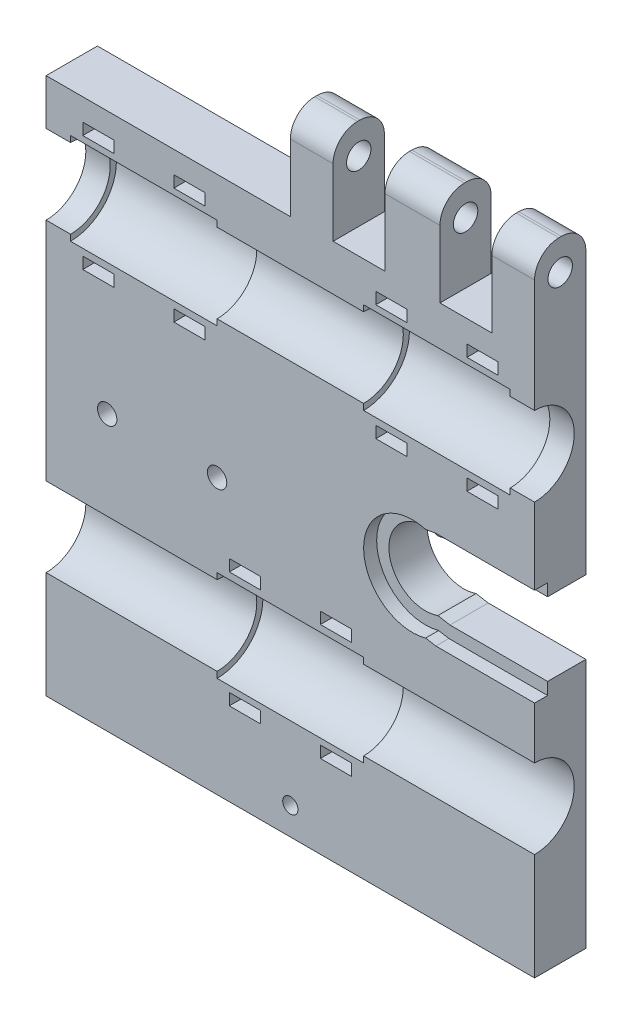
SolidWorks part; units mm, degrees
ref_plane "Front Plane" through (0, 0, 0) normal (0, 0, 1) x (1, 0, 0)
ref_plane "Top Plane" through (0, 0, 0) normal (0, 1, 0) x (1, 0, 0)
ref_plane "Right Plane" through (0, 0, 0) normal (1, 0, 0) x (0, 0, -1)
sketch "Sketch1" plane through (0, 0, 0) normal (0, 0, 1) x (1, 0, 0)
  line L1 (0, 0) -> (80, 0)
  line L2 (0, 0) -> (0, 78)
  line L3 (0, 78) -> (80, 78)
  line L4 (80, 0) -> (80, 78)
  dimension "D1" = 78
  dimension "D2" = 80
extrude "Boss-Extrude1" add sketch "Sketch1" along normal blind 8.4
sketch "Sketch2" plane through (0, 0, 8.4) normal (0, 0, 1) x (1, 0, 0)
  line L0 (0, 64) -> (80, 64)
  line L1 (0, 78) -> (0, 0) construction
  line L2 (80, 0) -> (80, 78) construction
  line L6 (80, 78) -> (0, 78) construction
  line L8 (0, 64) -> (9.5411, 64)
  line L9 (0, 64) -> (0, 70.5)
  line L10 (0, 70.5) -> (4, 70.5)
  line L12 (9.5411, 64) -> (23.4954, 64)
  line L13 (4, 70.5) -> (4, 71.5)
  line L14 (4, 71.5) -> (28, 71.5)
  line L15 (28, 70.5) -> (28, 71.5)
  line L16 (23.4954, 64) -> (54.4624, 64)
  line L18 (28, 70.5) -> (52, 70.5)
  line L20 (54.4624, 64) -> (68.2256, 64)
  line L21 (52, 70.5) -> (52, 71.5)
  line L22 (52, 71.5) -> (76, 71.5)
  line L23 (76, 70.5) -> (76, 71.5)
  line L24 (68.2256, 64) -> (80, 64)
  line L26 (76, 70.5) -> (80, 70.5)
  line L27 (80, 64) -> (80, 70.5)
  dimension "D1" = 7.5
  dimension "D2" = 14
  dimension "D3" = 6.5
  dimension "D4" = 24
  dimension "D5" = 24
  dimension "D6" = 4
  dimension "D7" = 4
revolve "Cut-Revolve1" cut sketch "Sketch2" angle 360 about L0
sketch "Sketch3" plane through (0, 0, 8.4) normal (0, 0, 1) x (1, 0, 0)
  line L0 (0, 14) -> (80, 14)
  line L1 (0, 57.5) -> (0, 0) construction
  line L2 (80, 0) -> (80, 57.5) construction
  line L3 (0, 0) -> (80, 0) construction
  line L4 (25.7093, 14) -> (47.9574, 14)
  line L5 (28, 20.5) -> (28, 21.5)
  line L6 (28, 21.5) -> (52, 21.5)
  line L7 (52, 20.5) -> (52, 21.5)
  line L8 (25.7093, 14) -> (0, 14)
  line L10 (28, 20.5) -> (0, 20.5)
  line L11 (0, 14) -> (0, 20.5)
  line L12 (47.9574, 14) -> (80, 14)
  line L14 (52, 20.5) -> (80, 20.5)
  line L15 (80, 14) -> (80, 20.5)
  dimension "D1" = 6.5
  dimension "D2" = 7.5
  dimension "D3" = 24
  dimension "D4" = 28
  dimension "D5" = 14
revolve "Cut-Revolve2" cut sketch "Sketch3" angle 360 about L0
sketch "Sketch4" plane through (0, 0, 8.4) normal (0, 0, 1) x (1, 0, 0)
  line L0 (0, 78) -> (0, 70.5) construction
  line L1 (6, 74.405) -> (11.08, 74.405)
  line L2 (6, 74.405) -> (6, 72.5)
  line L3 (6, 72.5) -> (11.08, 72.5)
  line L4 (11.08, 74.405) -> (11.08, 72.5)
  line L5 (20.92, 72.5) -> (26, 72.5)
  line L6 (20.92, 72.5) -> (20.92, 74.405)
  line L7 (20.92, 74.405) -> (26, 74.405)
  line L8 (26, 72.5) -> (26, 74.405)
  line L10 (28, 70.5) -> (28, 57.5) construction
  line L11 (80, 78) -> (0, 78) construction
  dimension "D1" = 5.08
  dimension "D2" = 5.08
  dimension "D3" = 1.905
  dimension "D4" = 1.905
  dimension "D5" = 6
  dimension "D6" = 2
  dimension "D7" = 5.5
extrude "Cut-Extrude1" cut sketch "Sketch4" against normal through all
pattern_linear "LPattern1" count 2 spacing 19 along (0, -1, 0) count 2 spacing 48 along (1, 0, 0) of "Cut-Extrude1"
sketch "Sketch5" plane through (0, 0, 8.4) normal (0, 0, 1) x (1, 0, 0)
  line L0 (28, 7.5) -> (28, 20.5) construction
  line L1 (30, 22.6) -> (35.08, 22.6)
  line L2 (30, 22.6) -> (30, 24.505)
  line L3 (30, 24.505) -> (35.08, 24.505)
  line L4 (35.08, 22.6) -> (35.08, 24.505)
  line L5 (44.92, 22.6) -> (50, 22.6)
  line L6 (44.92, 22.6) -> (44.92, 24.505)
  line L7 (44.92, 24.505) -> (50, 24.505)
  line L8 (50, 22.6) -> (50, 24.505)
  line L9 (52, 21.5) -> (52, 6.5) construction
  line L10 (28, 21.5) -> (52, 21.5) construction
  dimension "D1" = 2
  dimension "D2" = 2
  dimension "D3" = 5.08
  dimension "D4" = 5.08
  dimension "D5" = 1.1
  dimension "D6" = 1.1
  dimension "D7" = 1.905
  dimension "D8" = 1.905
extrude "Cut-Extrude2" cut sketch "Sketch5" against normal blind 8.4
pattern_linear "LPattern2" count 2 spacing 19 along (0, -1, 0) of "Cut-Extrude2"
sketch "Sketch6" plane through (0, 0, 8.4) normal (0, 0, 1) x (1, 0, 0)
  line L0 (0, 0) -> (80, 0) construction
  line L1 (80, 20.5) -> (80, 57.5) construction
  line L2 (60, 43) -> (80, 43)
  line L3 (80, 43) -> (80, 31)
  line L4 (80, 31) -> (60, 31)
  line L5 (64, 43) -> (62.0179, 42.6505)
  line L6 (64, 31) -> (62.0179, 31.3495)
  arc A0 (62.0179, 42.6505) -> (62.0179, 31.3495) centre (60, 37) ccw
  line M27 (80, 20.5) -> (80, 57.5)
  dimension "D1" = 12
  dimension "D2" = 37
  dimension "D3" = 20
  dimension "D4" = 4
  dimension "D5" = 170
  dimension "D6" = 4
  dimension "D7" = 170
extrude "Cut-Extrude3" cut sketch "Sketch6" against normal through all contours L5 A0 L6 L4 L2 M27
sketch "Sketch8" plane through (0, 0, 8.4) normal (0, 0, 1) x (1, 0, 0)
  line L12 (80, 45) -> (80, 29)
  line L16 (80, 29) -> (63.825, 29)
  line L17 (63.825, 29) -> (62.1523, 29.295)
  line L18 (63.825, 45) -> (80, 45)
  line L19 (62.1523, 44.705) -> (63.825, 45)
  line L20 (80, 29) -> (63.825, 29)
  line L21 (63.825, 29) -> (62.1523, 29.295)
  line L22 (63.825, 45) -> (80, 45)
  line L23 (62.1523, 44.705) -> (63.825, 45)
  arc A7 (62.1523, 44.705) -> (62.1523, 29.295) centre (60, 37) ccw
  arc A8 (62.1523, 44.705) -> (62.1523, 29.295) centre (60, 37) ccw
  dimension "D1" = 2
extrude "Cut-Extrude4" cut sketch "Sketch8" against normal blind 2.138
sketch "Sketch9" plane through (0, 0, 8.4) normal (0, 0, 1) x (1, 0, 0)
  line L0 (80, 78) -> (0, 78) construction
  line L1 (5, 39.5) -> (33, 39.5)
  line L2 (5, 39.5) -> (5, 46.5)
  line L3 (5, 46.5) -> (33, 46.5)
  line L4 (33, 39.5) -> (33, 46.5)
  line L5 (0, 57.5) -> (0, 20.5) construction
  line L6 (0, 0) -> (80, 0) construction
  circle A0 centre (10, 35) radius 1.5875
  circle A1 centre (28, 35) radius 1.5875
  dimension "D5" = 3.175
  dimension "D6" = 3.175
  dimension "D1" = 7
  dimension "D2" = 31.5
  dimension "D3" = 5
  dimension "D4" = 28
  dimension "D7" = 18
  dimension "D8" = 10
  dimension "D9" = 35
  dimension "D10" = 35
extrude "Cut-Extrude5" cut sketch "Sketch9" against normal through all contours A0 | A1
sketch "Sketch11" plane through (0, 0, 0) normal (0, -1, 0) x (-1, 0, 0)
  line L1 (0, -8.4) -> (-80, -8.4)
  line L2 (0, -8.4) -> (0, 0)
  line L3 (0, 0) -> (-80, 0)
  line L4 (-80, -8.4) -> (-80, 0)
extrude "Boss-Extrude3" add sketch "Sketch11" along normal blind 10
hole_wizard "Ø2.5 (2.5) Diameter Hole1" positions "Sketch13" profile "Sketch12" hole size "Ø2.5" standard "ANSI Metric"
sketch "Sketch13" plane through (0, 0, 8.4) normal (0, 0, 1) x (1, 0, 0)
  line L0 (28, 7.5) -> (28, 20.5) construction
  line L1 (80, -10) -> (80, 7.5) construction
  point P0 (40, -5.5)
  point P3 (28, 14)
  dimension "D1" = 19.5
  dimension "D2" = 40
sketch "Sketch12" plane through (40, -5.5, 8.4) normal (1, 0, 0) x (0, -1, 0)
  line L0 (0, 0) -> (0, 10)
  line L1 (0, 10) -> (1.25, 10)
  line L2 (1.25, 10) -> (1.25, 0)
  line L5 (1.25, 0) -> (0, 0)
  line L10 (0, 10) -> (-1.25, 10) construction
  line L11 (0, -6.35) -> (0, 107.95) construction
  dimension "Hole Dia." = 2.5
  dimension "Hole Depth" = 10
  dimension "Drill Angle" = 180
sketch "Sketch14" plane through (0, 78, 0) normal (0, 1, 0) x (1, 0, 0)
  line L0 (80, -8.4) -> (0, -8.4) construction
  line L1 (55.5, -8.4) -> (64.5, -8.4)
  line L2 (55.5, -8.4) -> (55.5, 0)
  line L3 (55.5, 0) -> (64.5, 0)
  line L4 (64.5, -8.4) -> (64.5, 0)
  line L5 (80, 0) -> (0, 0) construction
  line L6 (73, -8.4) -> (80, -8.4)
  line L7 (73, -8.4) -> (73, 0)
  line L8 (73, 0) -> (80, 0)
  line L9 (80, -8.4) -> (80, 0)
  line L10 (80, -8.4) -> (80, 0) construction
  line L11 (47, -8.4) -> (40, -8.4)
  line L12 (47, -8.4) -> (47, 0)
  line L13 (47, 0) -> (40, 0)
  line L14 (40, -8.4) -> (40, 0)
  dimension "D1" = 7
  dimension "D2" = 9
  dimension "D3" = 7
  dimension "D4" = 8.5
  dimension "D5" = 8.5
extrude "Boss-Extrude4" add sketch "Sketch14" along normal blind 15
ref_plane "Plane1" through (40, 93, 8.4) normal (0, 0, 1) x (1, 0, 0)
sketch "Sketch16" plane through (40, 0, 0) normal (-1, 0, 0) x (0, 0, 1)
  line L0 (0, 93) -> (8.4, 93) construction
  line L1 (0, 78) -> (8.4, 78) construction
  circle A0 centre (4.2, 88) radius 2
  point P2 (4.2, 93)
  dimension "D1" = 4
  dimension "D2" = 0
  dimension "D3" = 10
extrude "Cut-Extrude6" cut sketch "Sketch16" against normal blind 45.4
fillet "Fillet1" radius 4 6 edges at (76.5, 93, 8.4) (76.5, 93, 0) (60, 93, 8.4) (60, 93, 0) (43.5, 93, 8.4) (43.5, 93, 0)
